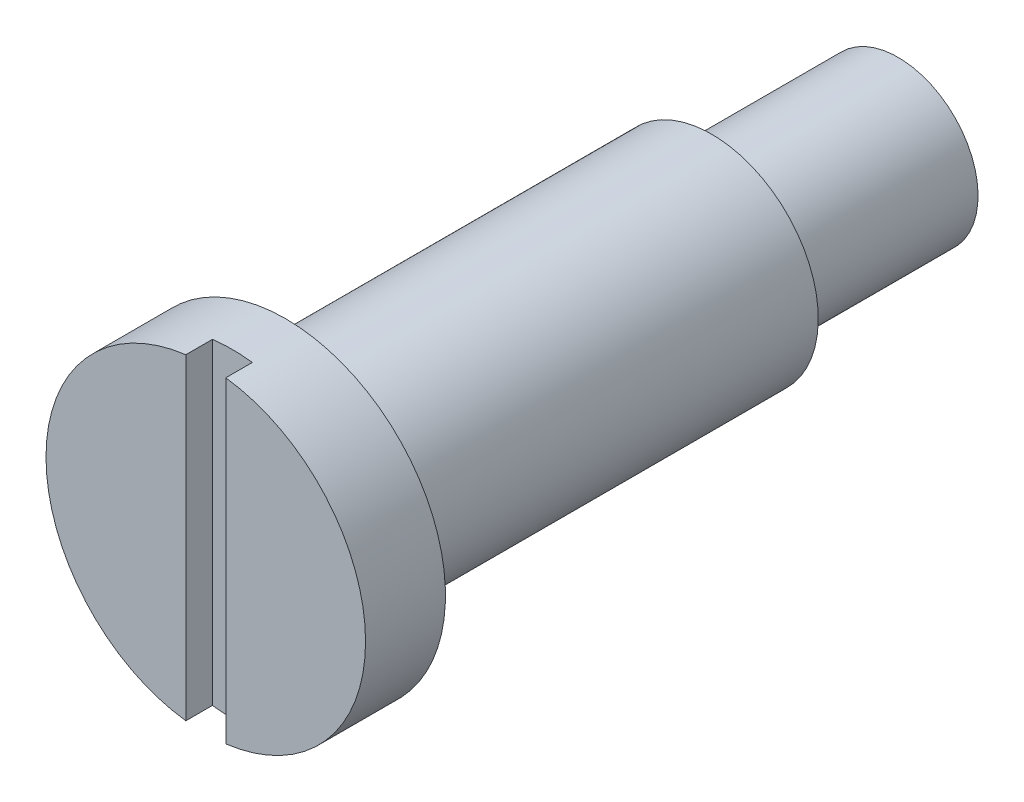
SolidWorks part; units mm, degrees
ref_plane "前视基准面" through (0, 0, 0) normal (0, 0, 1) x (1, 0, 0)
ref_plane "上视基准面" through (0, 0, 0) normal (0, 1, 0) x (1, 0, 0)
ref_plane "右视基准面" through (0, 0, 0) normal (1, 0, 0) x (0, 0, -1)
sketch "草图2" plane through (0, 0, 0) normal (1, 0, 0) x (0, 0, -1)
  line L0 (0, 0) -> (26, 0) construction
  line L1 (0, 0) -> (0, 6)
  line L2 (0, 6) -> (3, 6)
  line L3 (3, 6) -> (3, 4)
  line L4 (3, 4) -> (19, 4)
  line L5 (19, 4) -> (19, 3)
  line L6 (0, 0) -> (26, 0)
  line L7 (19, 3) -> (26, 3)
  line L8 (26, 3) -> (26, 0)
  line L10 (26, 0) -> (105.7683, 0) construction
  point P7 (19, 4)
  dimension "D1" = 12
  dimension "D2" = 16
  dimension "D3" = 3
  dimension "D4" = 8
  dimension "D5" = 6
  dimension "D6" = 7
revolve "旋转1" add sketch "草图2" angle 360 about L0
cosmetic thread "装饰螺纹线1" parameters "D1"=6.9999, "D2"=5
sketch "草图3" plane through (0, 0, 0) normal (0, 0, 1) x (1, 0, 0)
  line L1 (0.75, -6) -> (-0.75, -6)
  line L2 (0.75, -6) -> (0.75, 6)
  line L3 (0.75, 6) -> (-0.75, 6)
  line L4 (-0.75, -6) -> (-0.75, 6)
  line L5 (0.75, -6) -> (-0.75, 6) construction
  line L6 (0.75, 6) -> (-0.75, -6) construction
  circle A0 centre (0, 0) radius 6 construction
  point P0 (0, 0)
  dimension "D1" = 1.5
extrude "切除-拉伸1" cut sketch "草图3" against normal blind 1
